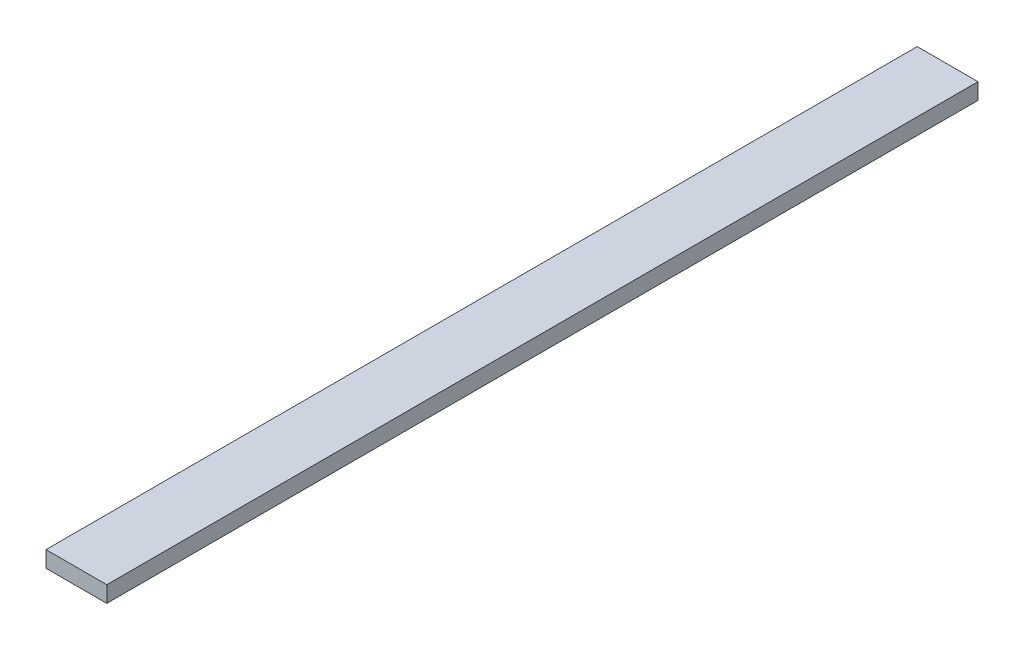
SolidWorks part; units mm, degrees
ref_plane "前视基准面" through (0, 0, 0) normal (0, 0, 1) x (1, 0, 0)
ref_plane "上视基准面" through (0, 0, 0) normal (0, 1, 0) x (1, 0, 0)
ref_plane "右视基准面" through (0, 0, 0) normal (1, 0, 0) x (0, 0, -1)
sketch "草图1" plane through (0, 0, 0) normal (0, 0, 1) x (1, 0, 0)
  line L1 (-15, 4) -> (15, 4)
  line L2 (-15, 4) -> (-15, -4)
  line L3 (-15, -4) -> (15, -4)
  line L4 (15, 4) -> (15, -4)
  line L5 (-15, 4) -> (15, -4) construction
  line L6 (-15, -4) -> (15, 4) construction
  point P0 (0, 0)
  dimension "D1" = 30
  dimension "D2" = 8
extrude "凸台-拉伸1" add sketch "草图1" along normal blind 430
